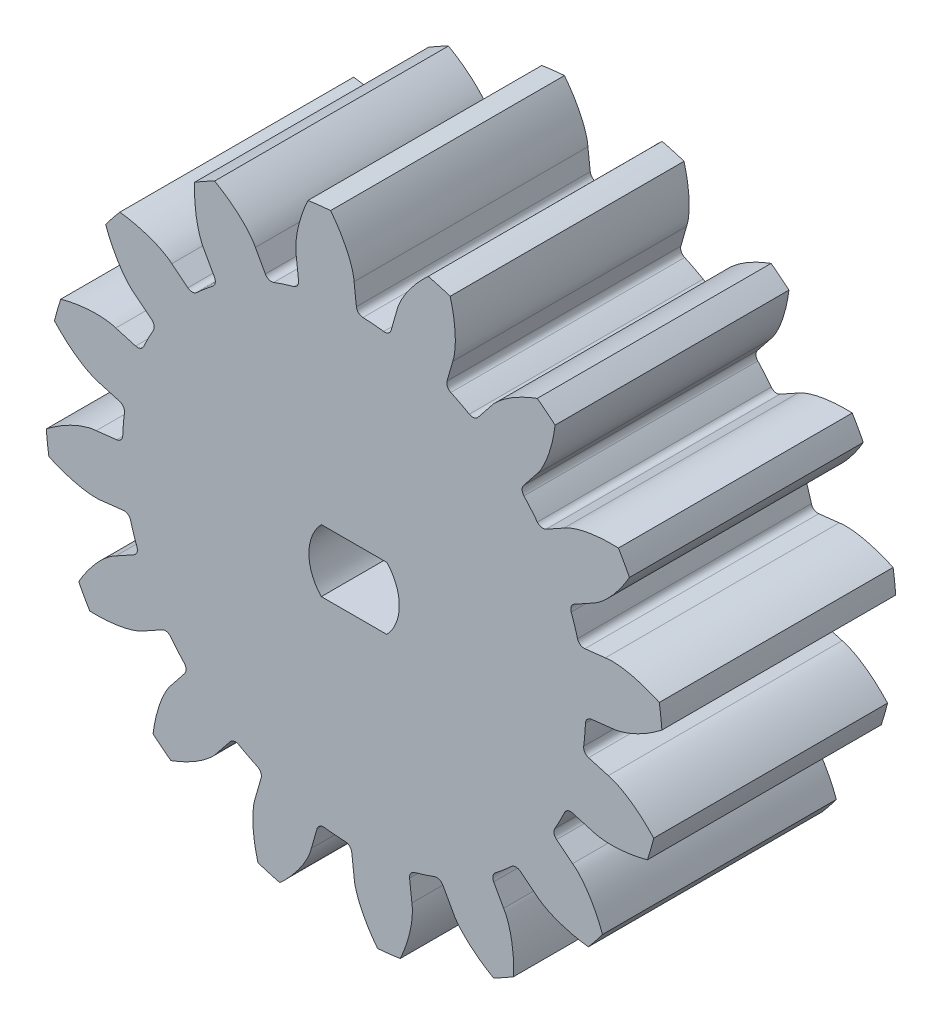
SolidWorks part; units mm, degrees
ref_plane "Front Plane" through (0, 0, 0) normal (0, 0, 1) x (1, 0, 0)
ref_plane "Top Plane" through (0, 0, 0) normal (0, 1, 0) x (1, 0, 0)
ref_plane "Right Plane" through (0, 0, 0) normal (1, 0, 0) x (0, 0, -1)
sketch "Sketch1" plane through (0, 0, 0) normal (0, 0, 1) x (1, 0, 0)
  line L0 (0, 0) -> (17.4876, 1.9859) construction
  circle A0 centre (0, 0) radius 14.85
  circle A1 centre (0, 0) radius 16.5386
  circle A2 centre (0, 0) radius 17.6 construction
  circle A3 centre (0, 0) radius 19.8
  arc A4 (17.598, 0.2622) -> (17.2087, 3.6904) centre (0, 0) ccw
  spline S0 degree 4 poles (16.5386, 0) (16.5896, 0.0022) (16.732, 0.0152) (17.0002, 0.0668) (17.4269, 0.1886) (17.9618, 0.4004) (18.6217, 0.7336) (19.354, 1.1964) (20.1087, 1.7762) (21.0528, 2.6441) (21.9015, 3.6071) (22.6879, 4.6841) (23.5094, 6.0441) (24.2176, 7.4675) (24.8829, 9.1906) (25.4296, 11.1688) (25.7926, 13.1885) (25.9803, 15.2316) (26.0013, 17.2829) (25.8634, 19.3296) (25.5749, 21.3601) (25.2241, 22.9895) (24.891, 24.2262) (24.5913, 25.2068) (24.3915, 25.8135) (24.1763, 26.4205) (23.952, 27.0145) (23.7591, 27.4994) (23.5866, 27.9162) (23.4131, 28.3176) (23.2004, 28.7942) (23.0461, 29.1256) (22.775, 29.6933) (22.5336, 30.1653) (22.2662, 30.6834) (22.0634, 31.0486) (21.8496, 31.4328) (21.7512, 31.6022) (21.6988, 31.693) (21.6721, 31.7392) knots 0 0 0 0 0 0.005604 0.015718 0.02996 0.048734 0.068727 0.096889 0.125051 0.153212 0.209535 0.237696 0.271429 0.327752 0.384075 0.440398 0.496721 0.553044 0.609367 0.66569 0.722013 0.778336 0.792417 0.806497 0.834659 0.84874 0.86282 0.876901 0.890982 0.900036 0.909091 0.931818 0.943182 0.954545 0.977273 0.988636 0.994318 1 1 1 1 1 construction
  spline S1 degree 4 poles (16.5386, 0) (16.5896, 0.0022) (16.732, 0.0152) (17.0002, 0.0668) (17.4269, 0.1886) (17.9618, 0.4004) (18.6217, 0.7336) (19.354, 1.1964) (20.1087, 1.7762) (21.0528, 2.6441) (21.9015, 3.6071) (22.6879, 4.6841) (23.5094, 6.0441) (24.2176, 7.4675) (24.8829, 9.1906) (25.4296, 11.1688) (25.7926, 13.1885) (25.9803, 15.2316) (26.0013, 17.2829) (25.8634, 19.3296) (25.5749, 21.3601) (25.2241, 22.9895) (24.891, 24.2262) (24.5913, 25.2068) (24.3915, 25.8135) (24.1763, 26.4205) (23.952, 27.0145) (23.7591, 27.4994) (23.5866, 27.9162) (23.4131, 28.3176) (23.2884, 28.5969) (23.2257, 28.7354) (23.1945, 28.8035) knots 0 0 0 0 0 0.005604 0.015718 0.02996 0.048734 0.068727 0.096889 0.125051 0.153212 0.209535 0.237696 0.271429 0.327752 0.384075 0.440398 0.496721 0.553044 0.609367 0.66569 0.722013 0.778336 0.792417 0.806497 0.834659 0.84874 0.86282 0.876901 0.890982 0.900036 0.909091 0.909091 0.909091 0.909091 0.909091
  dimension "D1" = 29.7
  dimension "D2" = 33.0772
  dimension "D3" = 35.2
  dimension "D4" = 39.6
  dimension "D5" = 3.4558
extrude "Boss-Extrude1" add sketch "Sketch1" along normal mid plane 15 contours A0
sketch "Sketch4" plane through (0, 0, 0) normal (0, 0, 1) x (1, 0, 0)
  line L0 (0, 0) -> (17.4876, 1.9859) construction
  line L1 (0, 0) -> (17.4876, 1.9859) construction
  line L2 (16.5386, 0) -> (14.8488, -0.1919)
  line L3 (16.1175, 3.7084) -> (14.4276, 3.5165)
  circle A0 centre (0, 0) radius 16.5386 construction
  circle A1 centre (0, 0) radius 14.85 construction
  circle A2 centre (0, 0) radius 16.5386
  circle A3 centre (0, 0) radius 14.85
extrude "Boss-Extrude2" add sketch "Sketch4" along normal mid plane 15 contours L1 A3 L2 A2 | A3 L1 A2 L3
sketch "Sketch6" plane through (0, 0, 0) normal (0, 0, 1) x (1, 0, 0)
  line L1 (0, 0) -> (17.4876, 1.9859) construction
  line L2 (0, 0) -> (17.4876, 1.9859) construction
  circle A0 centre (0, 0) radius 16.5386 construction
  circle A2 centre (0, 0) radius 16.5386
  circle A4 centre (0, 0) radius 19.8 construction
  circle A5 centre (0, 0) radius 19.8
  spline S1 degree 4 poles (6.0697, 1999.7783) (8.2632, 43.5108) (11.7046, 0.8342) (14.755, -0.5737) (17.4269, 0.1886) (17.9618, 0.4004) (18.6217, 0.7336) (19.354, 1.1964) (20.1087, 1.7762) (21.0528, 2.6441) (21.9015, 3.6071) (22.6879, 4.6841) (23.5094, 6.0441) (24.2176, 7.4675) (24.8829, 9.1906) (25.4296, 11.1688) (25.7926, 13.1885) (25.9803, 15.2316) (26.0013, 17.2829) (25.8634, 19.3296) (25.5749, 21.3601) (25.2241, 22.9895) (24.891, 24.2262) (24.5913, 25.2068) (24.3915, 25.8135) (24.1763, 26.4205) (23.952, 27.0145) (23.7591, 27.4994) (23.5866, 27.9162) (22.632, 30.1239) (21.5135, 32.2158) (37.0232, -2.3928) (-809.7272, 1846.767) knots -0.256426 -0.256426 -0.256426 -0.256426 -0.256426 0.005604 0.015718 0.02996 0.048734 0.068727 0.096889 0.125051 0.153212 0.209535 0.237696 0.271429 0.327752 0.384075 0.440398 0.496721 0.553044 0.609367 0.66569 0.722013 0.778336 0.792417 0.806497 0.834659 0.84874 0.86282 0.876901 0.890982 0.900036 1.117323 1.117323 1.117323 1.117323 1.117323 only from (16.5386, 0) to (23.1945, 28.8035) construction
  spline S2 degree 4 poles (16.5386, 0) (16.5896, 0.0022) (16.732, 0.0152) (17.0002, 0.0668) (17.4269, 0.1886) (17.9618, 0.4004) (18.6217, 0.7336) (19.354, 1.1964) (20.1087, 1.7762) (21.0528, 2.6441) (21.9015, 3.6071) (22.6879, 4.6841) (23.5094, 6.0441) (24.2176, 7.4675) (24.8829, 9.1906) (25.4296, 11.1688) (25.7926, 13.1885) (25.9803, 15.2316) (26.0013, 17.2829) (25.8634, 19.3296) (25.5749, 21.3601) (25.2241, 22.9895) (24.891, 24.2262) (24.5913, 25.2068) (24.3915, 25.8135) (24.1763, 26.4205) (23.952, 27.0145) (23.7591, 27.4994) (23.5866, 27.9162) (23.4131, 28.3176) (23.2884, 28.5969) (23.2257, 28.7354) (23.1945, 28.8035) knots 0 0 0 0 0 0.005604 0.015718 0.02996 0.048734 0.068727 0.096889 0.125051 0.153212 0.209535 0.237696 0.271429 0.327752 0.384075 0.440398 0.496721 0.553044 0.609367 0.66569 0.722013 0.778336 0.792417 0.806497 0.834659 0.84874 0.86282 0.876901 0.890982 0.900036 0.909091 0.909091 0.909091 0.909091 0.909091
  spline S3 degree 4 poles (16.1175, 3.7084) (16.1676, 3.7177) (16.3093, 3.7369) (16.5823, 3.7468) (17.0255, 3.7238) (17.5942, 3.6373) (18.312, 3.4606) (19.1295, 3.1737) (19.995, 2.778) (21.1096, 2.1439) (22.1526, 1.3957) (23.1605, 0.5224) (24.266, -0.6187) (25.2754, -1.8471) (26.3101, -3.3772) (27.2865, -5.1824) (28.0931, -7.0692) (28.7341, -9.0182) (29.2145, -11.0126) (29.5391, -13.0381) (29.7132, -15.0816) (29.7367, -16.7481) (29.6894, -18.0281) (29.6172, -19.0509) (29.5585, -19.687) (29.4849, -20.3267) (29.3995, -20.9559) (29.3202, -21.4718) (29.2456, -21.9166) (29.1665, -22.3467) (29.1077, -22.6468) (29.0775, -22.7958) (29.0624, -22.8692) knots 0 0 0 0 0 0.005604 0.015718 0.02996 0.048734 0.068727 0.096889 0.125051 0.153212 0.209535 0.237696 0.271429 0.327752 0.384075 0.440398 0.496721 0.553044 0.609367 0.66569 0.722013 0.778336 0.792417 0.806497 0.834659 0.84874 0.86282 0.876901 0.890982 0.900036 0.909091 0.909091 0.909091 0.909091 0.909091
extrude "Boss-Extrude3" add sketch "Sketch6" along normal mid plane 15
fillet "Fillet1" radius 0.44 2 edges at (14.8488, -0.1919, 0) (14.4276, 3.5165, 0)
pattern_circular "CirPattern1" count 16 over 360 about axis through (0, 0, 7.5) along (0, 0, -1) of "Boss-Extrude3", "Boss-Extrude2", "Fillet1"
fillet "Fillet2" [suppressed] radius 0.44
pattern_circular "CirPattern2" [suppressed] count 16 over 360
sketch "Sketch7" plane through (0, 0, 7.5) normal (0, 0, 1) x (1, 0, 0)
  line L0 (-2.1, 2) -> (2.1, 2)
  line L7 (-2.1, -2) -> (2.1, -2)
  circle A0 centre (0, 0) radius 2.9
  dimension "D1" = 5.8
  dimension "D2" = 4
extrude "Cut-Extrude1" cut sketch "Sketch7" against normal blind 8 contours L0 A0 L7
sketch "Sketch8" plane through (0, 0, -7.5) normal (0, 0, -1) x (-1, 0, 0)
  circle A0 centre (0, 0) radius 3.25
  dimension "D1" = 6.5
extrude "Cut-Extrude3" cut sketch "Sketch8" against normal up to surface (7 mm away) up to face at (0, 0, -0.5)
equation "\"m\"= 2.2'Модуль"
equation "\"z\"= 16'Число зубьев"
equation "\"b\"= 15mm'Ширина зубчатого венца"
equation "\"a\"= 20 * pi / 180'Угол профиля исходного контура"
equation "\"D\"= \"m\" * \"z\"'Диаметр делительной окружности"
equation "\"Db\"= \"D\" * cos ( \"a\" )'Диаметр начальной окружности"
equation "\"Da\"= \"D\" + \"m\" * 2'Диаметр вершин зубьев"
equation "\"Df\"= \"D\" - \"m\" * 2.5'Диаметр впадин зубьев"
equation "\"S\"= \"m\" * pi / 2'Толщина зуба по дуге"
equation "\"D1@Sketch1\"= \"Df\""
equation "\"D2@Sketch1\"=\"Db\""
equation "\"D3@Sketch1\"=\"D\""
equation "\"D4@Sketch1\"=\"Da\""
equation "\"D1@Boss-Extrude1\"=\"b\""
equation "\"D5@Sketch1\"=\"S\""
equation "\"D1@Boss-Extrude2\"=\"b\""
equation "\"D1@Boss-Extrude3\"=\"b\""
equation "\"D1@Fillet1\"=\"m\"*0.2"
equation "\"D1@CirPattern1\"=\"z\""
equation "\"Fillet1\"= IIF ( \"Df\" > \"Db\" , \"suppressed\" , \"unsuppressed\" )"
equation "\"CirPattern1\"= IIF ( \"Df\" > \"Db\" , \"suppressed\" , \"unsuppressed\" )"
equation "\"D1@Fillet2\"=\"m\"*0.2"
equation "\"D1@CirPattern2\"=\"z\""
equation "\"Fillet2\"= IIF ( \"Db\" > \"Df\" , \"suppressed\" , \"unsuppressed\" )"
equation "\"CirPattern2\"= IIF ( \"Db\" > \"Df\" , \"suppressed\" , \"unsuppressed\" )"
